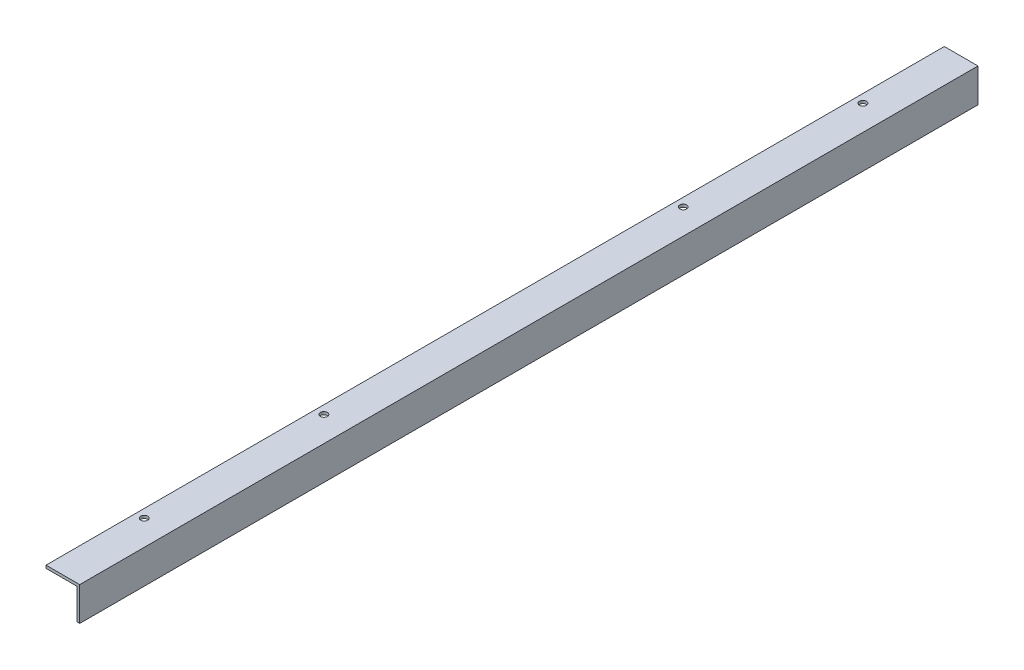
SolidWorks part; units mm, degrees
material "6063-T6"
ref_plane "Front Plane" through (0, 0, 0) normal (0, 0, 1) x (1, 0, 0)
ref_plane "Top Plane" through (0, 0, 0) normal (0, 1, 0) x (1, 0, 0)
ref_plane "Right Plane" through (0, 0, 0) normal (1, 0, 0) x (0, 0, -1)
sketch "Sketch1" plane through (0, 0, 0) normal (0, 0, 1) x (1, 0, 0)
  line L0 (0, 0) -> (-38.1, 0)
  line L1 (-38.1, 0) -> (-38.1, -3.175)
  line L2 (-38.1, -3.175) -> (-3.175, -3.175)
  line L3 (-3.175, -3.175) -> (-3.175, -38.1)
  line L4 (-3.175, -38.1) -> (0, -38.1)
  line L5 (0, -38.1) -> (0, 0)
  dimension "D1" = 38.1
  dimension "D2" = 3.175
extrude "Boss-Extrude1" add sketch "Sketch1" along normal blind 1016
extrude "Cut-Extrude3" cut sketch "Sketch4" against normal blind 44.45
sketch "Sketch4" plane through (10.6701, 3.175, 791.5633) normal (0, 1, 0) x (1, 0, 0)
  circle A0 centre (-39.2451, 689.9633) radius 3.9687
pattern_linear "LPattern1" count 5 spacing 203.2 along (0, 0, 1) skipping (2, 0) of "Cut-Extrude3"
